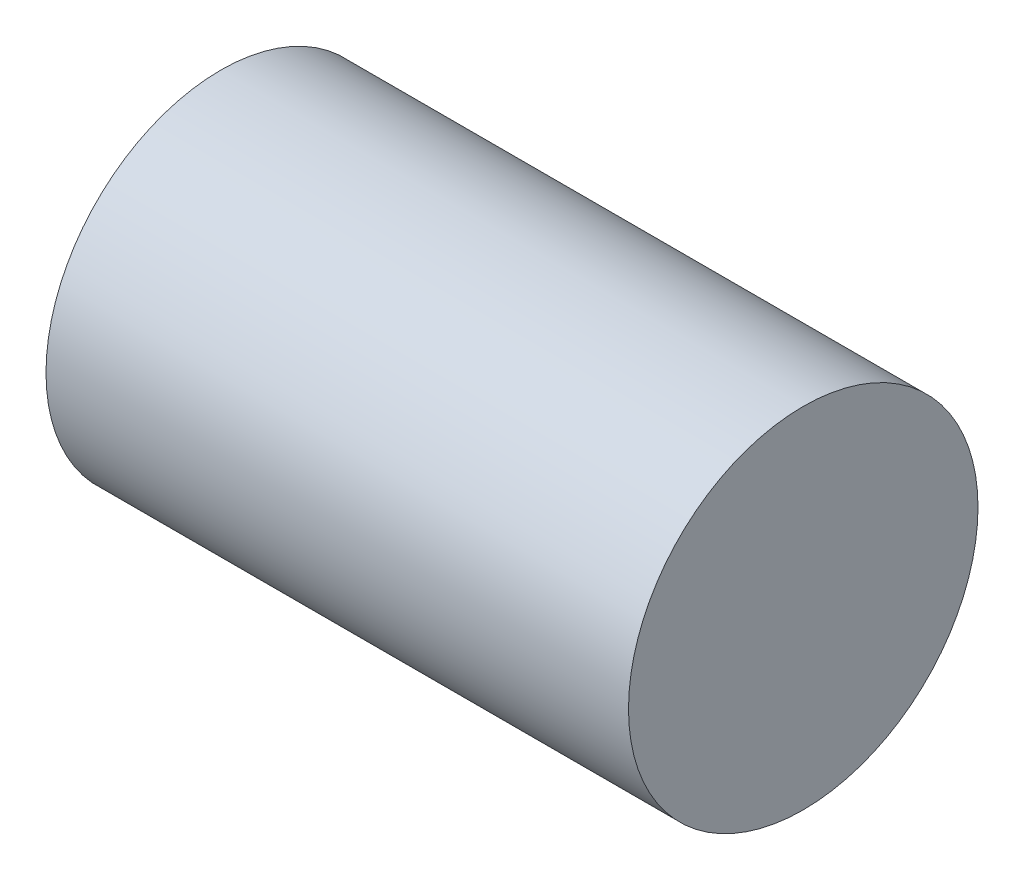
SolidWorks part; units mm, degrees
material "1060 Alloy"
ref_plane "Front" through (0, 0, 0) normal (0, 0, 1) x (1, 0, 0)
ref_plane "Top" through (0, 0, 0) normal (0, 1, 0) x (1, 0, 0)
ref_plane "Right" through (0, 0, 0) normal (1, 0, 0) x (0, 0, -1)
sketch "Sketch1" plane through (0, 0, 0) normal (1, 0, 0) x (0, 0, -1)
  circle A0 centre (0, 0) radius 3.75
  dimension "D1" = 7.5
extrude "Boss-Extrude1" add sketch "Sketch1" along normal blind 12.5
